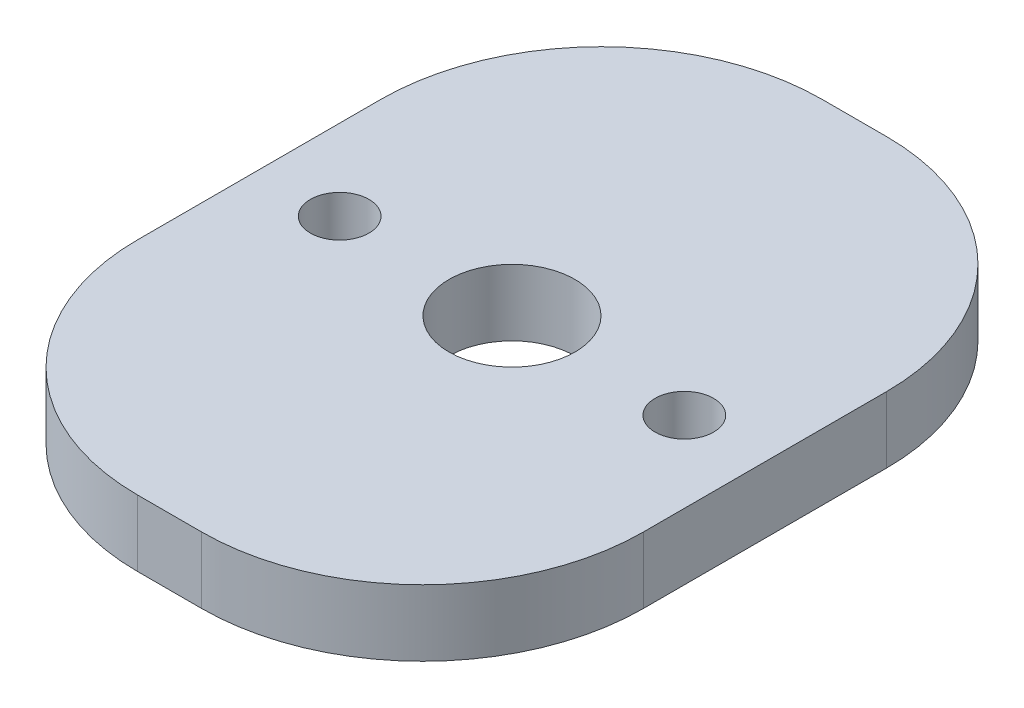
SolidWorks part; units mm, degrees
ref_plane "Front Plane" through (0, 0, 0) normal (0, 0, 1) x (1, 0, 0)
ref_plane "Top Plane" through (0, 0, 0) normal (0, 1, 0) x (1, 0, 0)
ref_plane "Right Plane" through (0, 0, 0) normal (1, 0, 0) x (0, 0, -1)
sketch "Sketch1" plane through (0, 0, 0) normal (0, 1, 0) x (1, 0, 0)
  line L0 (-7.8, 0) -> (7.8, 0) construction
  line L2 (-1.45, 15.5) -> (1.45, 15.5)
  line L3 (-11.45, 5.5) -> (-11.45, -5.5)
  line L4 (-1.45, -15.5) -> (1.45, -15.5)
  line L5 (11.45, 5.5) -> (11.45, -5.5)
  line L6 (-8.9495, 12.115) -> (8.9495, -12.115) construction
  line L7 (-8.9495, -12.115) -> (8.9495, 12.115) construction
  circle A0 centre (7.8, 0) radius 1.325
  circle A1 centre (-7.8, 0) radius 1.325
  circle A2 centre (0, 0) radius 2.85
  arc A3 (11.45, -5.5) -> (1.45, -15.5) centre (1.45, -5.5) cw
  arc A4 (-1.45, -15.5) -> (-11.45, -5.5) centre (-1.45, -5.5) cw
  arc A5 (-1.45, 15.5) -> (-11.45, 5.5) centre (-1.45, 5.5) ccw
  arc A6 (1.45, 15.5) -> (11.45, 5.5) centre (1.45, 5.5) cw
  point P4 (0, 0)
  dimension "D2" = 2.65
  dimension "D3" = 2.65
  dimension "D4" = 5.7
  dimension "D7" = 10
  dimension "D1" = 15.6
  dimension "D5" = 15.5
  dimension "D6" = 3.65
extrude "Boss-Extrude1" add sketch "Sketch1" along normal blind 3
